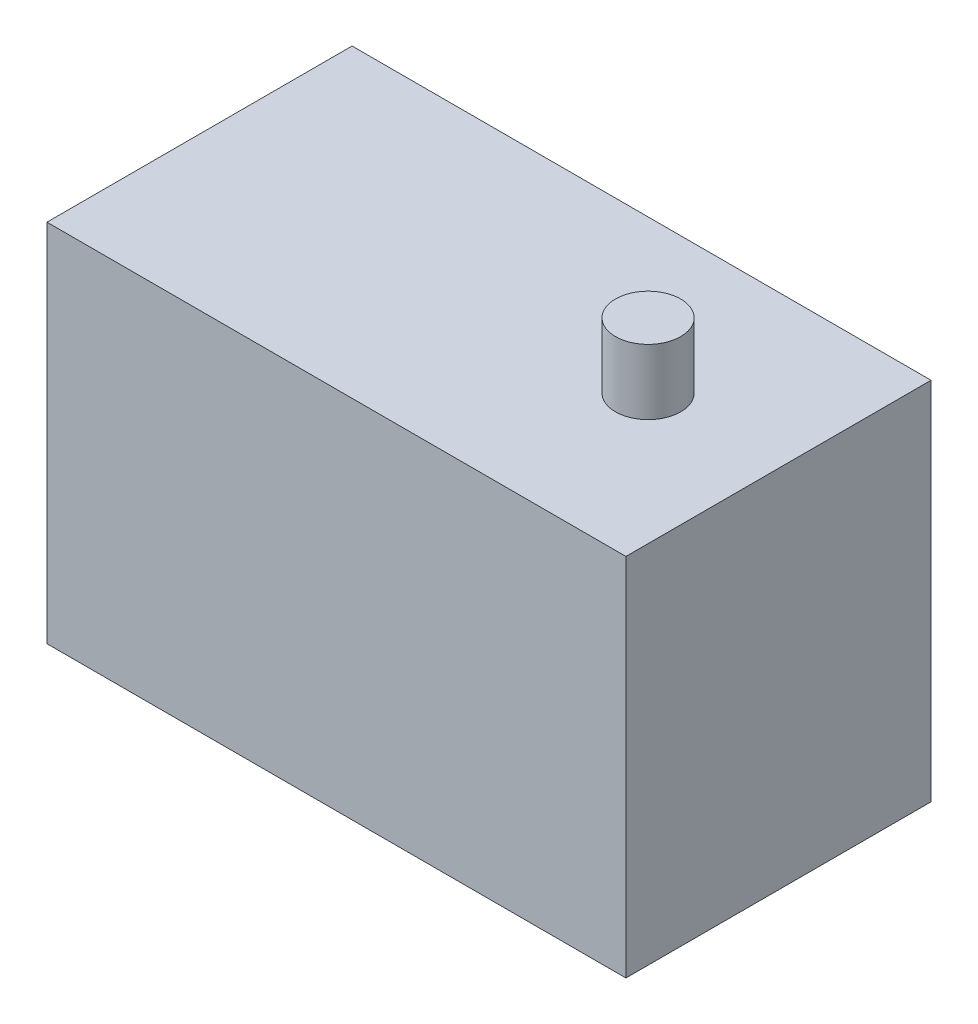
SolidWorks part; units mm, degrees
ref_plane "前基準面" through (0, 0, 0) normal (0, 0, 1) x (1, 0, 0)
ref_plane "上基準面" through (0, 0, 0) normal (0, 1, 0) x (1, 0, 0)
ref_plane "右基準面" through (0, 0, 0) normal (1, 0, 0) x (0, 0, -1)
sketch "草圖1" plane through (0, 0, 0) normal (0, 1, 0) x (1, 0, 0)
  line L0 (-42.1478, 23.1931) -> (2.2522, 23.1931)
  line L2 (-42.1478, 23.1931) -> (-42.1478, -0.2069)
  line L3 (-42.1478, -0.2069) -> (2.2522, -0.2069)
  line L4 (2.2522, 23.1931) -> (2.2522, -0.2069)
  line L5 (-42.1478, 11.4931) -> (2.2522, 11.4931) construction
  dimension "D1" = 23.4
  dimension "D2" = 44.4
  dimension "D3" = 11.7
extrude "填料-伸長1" add sketch "草圖1" along normal blind 28
sketch "草圖2" plane through (0, 0, 0) normal (0, 1, 0) x (1, 0, 0)
  line L0 (-42.1478, 11.4931) -> (2.2522, 11.4931) construction
  line L1 (-42.1478, 23.1931) -> (-42.1478, -0.2069) construction
  line L2 (2.2522, -0.2069) -> (2.2522, 23.1931) construction
  circle A0 centre (-7.7478, 11.4931) radius 2.5
  dimension "D2" = 5
  dimension "D1" = 10
extrude "填料-伸長2" add sketch "草圖2" against normal blind 5 contours A0
pattern_linear "直線複製排列1" count 2 spacing 33 along (0, 1, 0) of "填料-伸長2"
